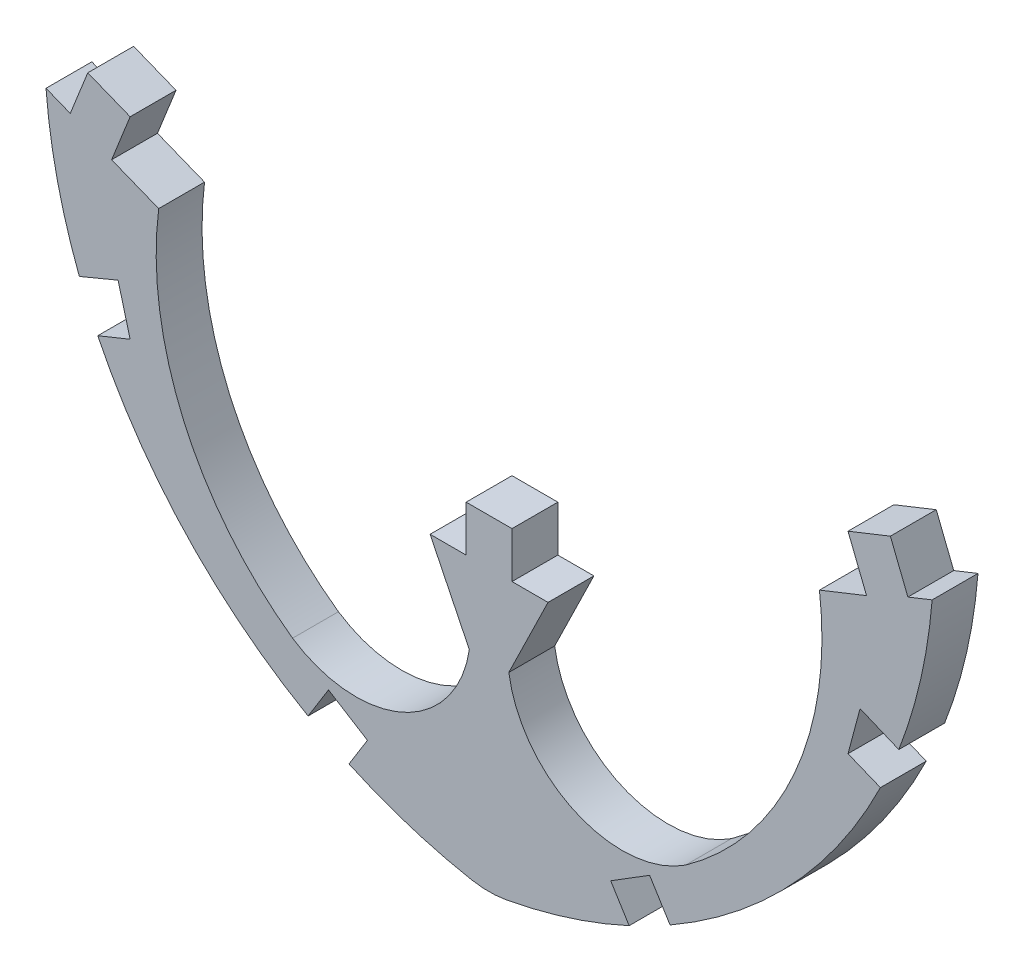
SolidWorks part; units mm, degrees
ref_plane "Front Plane" through (0, 0, 0) normal (0, 0, 1) x (1, 0, 0)
ref_plane "Top Plane" through (0, 0, 0) normal (0, 1, 0) x (1, 0, 0)
ref_plane "Right Plane" through (0, 0, 0) normal (1, 0, 0) x (0, 0, -1)
sketch "Sketch1" plane through (0, 0, 0) normal (0, 0, 1) x (1, 0, 0)
  line L0 (106.8002, 0) -> (106.8002, -1.524)
  line L1 (106.8002, -1.524) -> (105.6023, -1.524)
  line L2 (105.6023, -1.524) -> (106.9067, -4.1932)
  line L3 (96.5813, 3.3399) -> (95.0169, 3.9632)
  line L4 (95.0169, 3.9632) -> (95.633, 5.5093)
  line L5 (95.633, 5.5093) -> (94.2249, 6.0704)
  line L6 (94.2249, 6.0704) -> (93.6427, 4.6093)
  line L7 (93.6427, 4.6093) -> (92.8365, 4.9305)
  line L8 (106.8002, 0) -> (108.3242, 0)
  line L9 (120.5682, -1.3318) -> (119.4913, -0.8951)
  line L10 (121.1797, 0.0685) -> (119.8925, 0.604)
  line L11 (121.4817, 4.6093) -> (122.2878, 4.9305)
  line L12 (120.8994, 6.0704) -> (121.4817, 4.6093)
  line L13 (119.4913, 5.5093) -> (120.8994, 6.0704)
  line L14 (120.1074, 3.9632) -> (119.4913, 5.5093)
  line L15 (118.543, 3.3399) -> (120.1074, 3.9632)
  line L16 (109.522, -1.524) -> (108.2176, -4.1932)
  line L17 (108.3242, -1.524) -> (109.522, -1.524)
  line L18 (108.3242, 0) -> (108.3242, -1.524)
  line L19 (107.5622, -10.8334) -> (107.5622, -17.4203) construction
  line L21 (119.4913, -0.8951) -> (119.8925, 0.604)
  line L22 (113.5773, -8.7825) -> (112.8989, -7.691)
  line L23 (112.2179, -9.4823) -> (111.6046, -8.4955)
  line L24 (102.9064, -9.4823) -> (103.5197, -8.4955)
  line L25 (112.8989, -7.691) -> (111.6046, -8.4955)
  line L26 (102.2254, -7.691) -> (103.5197, -8.4955)
  line L27 (101.547, -8.7825) -> (102.2254, -7.691)
  line L28 (94.5561, -1.3318) -> (95.633, -0.8951)
  line L29 (95.633, -0.8951) -> (95.2319, 0.604)
  line L30 (93.9446, 0.0685) -> (95.2319, 0.604)
  arc A0 (106.9067, -4.1932) -> (101.0315, -6.8007) centre (103.1372, -3.6224) cw
  arc A1 (101.0315, -6.8007) -> (96.5813, 3.3399) centre (107.31, 2.0014) cw
  arc A2 (92.8365, 4.9305) -> (93.9446, 0.0685) centre (110.1844, 6.3269) ccw
  arc A3 (122.2878, 4.9305) -> (121.1797, 0.0685) centre (104.9399, 6.3269) cw
  arc A4 (114.0928, -6.8007) -> (118.543, 3.3399) centre (107.8143, 2.0014) ccw
  arc A5 (108.2176, -4.1932) -> (114.0928, -6.8007) centre (111.9871, -3.6224) ccw
  arc A6 (106.977, -10.779) -> (108.1473, -10.779) centre (107.5622, -7.6584) ccw
  arc A7 (120.5682, -1.3318) -> (113.5773, -8.7825) centre (104.9399, 6.3269) cw
  arc A8 (112.2179, -9.4823) -> (108.1473, -10.779) centre (104.9399, 6.3269) cw
  arc A9 (102.9064, -9.4823) -> (106.977, -10.779) centre (110.1844, 6.3269) ccw
  arc A10 (94.5561, -1.3318) -> (101.547, -8.7825) centre (110.1844, 6.3269) ccw
  dimension "D1" = 3.175
extrude "Boss-Extrude1" add sketch "Sketch1" along normal blind 1.524
